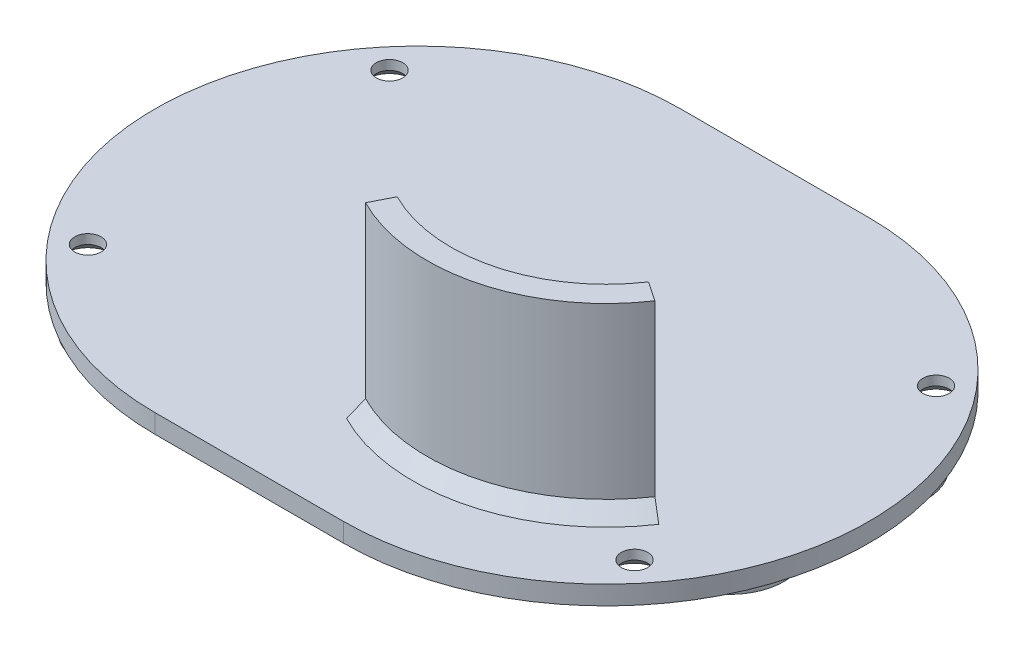
SolidWorks part; units mm, degrees
ref_plane "Front Plane" through (0, 0, 0) normal (0, 0, 1) x (1, 0, 0)
ref_plane "Top Plane" through (0, 0, 0) normal (0, 1, 0) x (1, 0, 0)
ref_plane "Right Plane" through (0, 0, 0) normal (1, 0, 0) x (0, 0, -1)
sketch "Sketch1" plane through (0, 2, 0) normal (0, -1, 0) x (1, 0, 0)
  line L0 (0, -27.9) -> (20, -27.9)
  line L1 (20, 27.9) -> (0, 27.9)
  line L4 (0, -28) -> (20, -28) construction
  line L5 (20, 28) -> (0, 28) construction
  arc A0 (20, -27.9) -> (20, 27.9) centre (20, 0) ccw
  arc A1 (0, 27.9) -> (0, -27.9) centre (0, 0) ccw
  arc A4 (0, 28) -> (0, -28) centre (0, 0) ccw construction
  arc A5 (20, -28) -> (20, 28) centre (20, 0) ccw construction
  dimension "D2" = 0.1
extrude "Boss-Extrude1" add sketch "Sketch1" along normal blind 2
sketch "Sketch8" plane through (0, 2, 0) normal (0, 1, 0) x (1, 0, 0)
  arc A0 (33.693, -9.206) -> (12.5325, -14.7135) centre (20, 0) cw
  dimension "D1" = 16.5
extrude "Extrude-Thin2" add sketch "Sketch8" along normal blind 19.5 thin thin type one direction reverse wall 2.5
chamfer "Chamfer1" distance 1.5 angle 45 2 edges at (24.7857, 2, 18.3874) (24.156, 2, 15.968)
hole_wizard "CSK for ST2.2 Cross recessed CTSK head tapping screws1" positions "Sketch2" profile "Sketch3" countersink size "ST2.2" standard "GB"
sketch "Sketch2" plane through (0, 0, 0) normal (0, -1, 0) x (-1, 0, 0)
  line L0 (0, 0) -> (-20, 0) construction
  line L3 (-39, 16) -> (19, 16)
  line L4 (-39, 16) -> (-39, -16)
  line L5 (-39, -16) -> (19, -16)
  line L6 (19, 16) -> (19, -16)
  line L7 (-10, 0) -> (-10, 22.0512) construction
  point P0 (-39, 16)
  point P2 (-39, -16)
  point P4 (19, -16)
  point P6 (19, 16)
  dimension "D1" = 32
  dimension "D2" = 58
sketch "Sketch3" plane through (39, 0, -16) normal (1, 0, 0) x (0, 0, -1)
  line L0 (0, 0) -> (0, 8.3412)
  line L1 (0, 8.3412) -> (1.4, 7.5)
  line L2 (1.4, 7.5) -> (1.4, 1)
  line L3 (1.4, 1) -> (2.4, 0)
  line L5 (2.4, 0) -> (0, 0)
  line L6 (-1.4, 1) -> (-2.4, 0) construction
  line L10 (0, 8.3412) -> (-1.4, 7.5) construction
  line L11 (0, -6.35) -> (0, 107.95) construction
  dimension "Hole Dia." = 2.8
  dimension "Hole Depth" = 7.5
  dimension "Near C'Sink Dia." = 4.8
  dimension "Near C'Sink Angle" = 90
  dimension "Drill Angle" = 118
sketch "Sketch4" plane through (0, 0, 0) normal (0, -1, 0) x (1, 0, 0)
  circle A0 centre (-11, 19.0526) radius 4.25
  circle A1 centre (-11, -19.0526) radius 4.25
  circle A2 centre (40.6732, 7.5244) radius 4.25
  circle A3 centre (40.6732, -7.5244) radius 4.25
  dimension "D1" = 8.5
extrude "Extrude-Thin1" add sketch "Sketch4" along normal blind 0.5 thin
